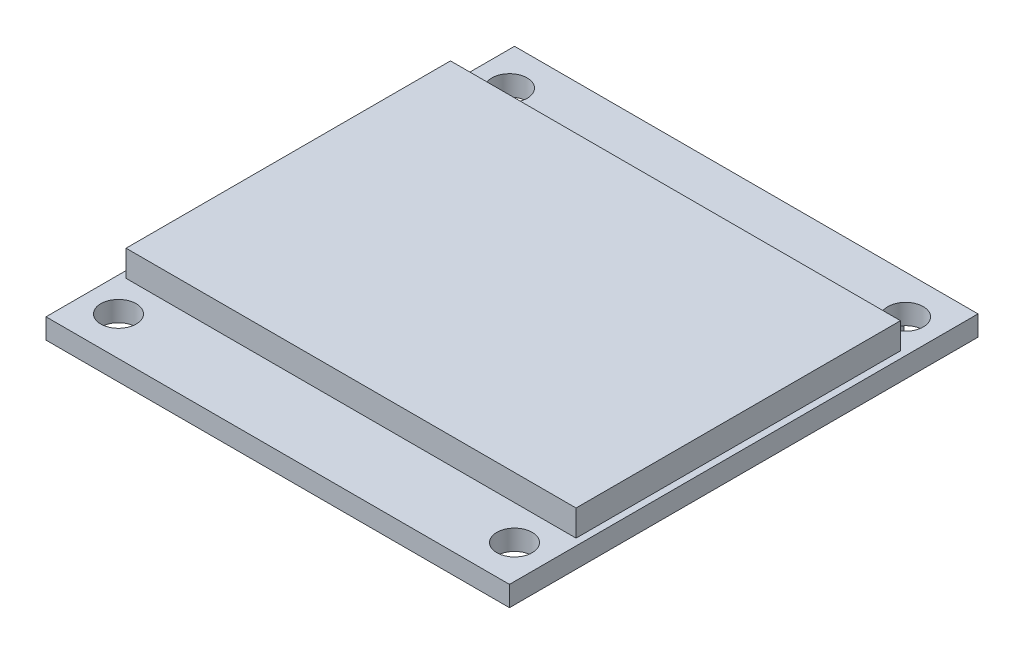
SolidWorks part; units mm, degrees
ref_plane "Front Plane" through (0, 0, 0) normal (0, 0, 1) x (1, 0, 0)
ref_plane "Top Plane" through (0, 0, 0) normal (0, 1, 0) x (1, 0, 0)
ref_plane "Right Plane" through (0, 0, 0) normal (1, 0, 0) x (0, 0, -1)
sketch "Sketch1" plane through (0, 0, 0) normal (0, 1, 0) x (1, 0, 0)
  line L1 (-21.737, 17.9787) -> (5.763, 17.9787)
  line L2 (-21.737, 17.9787) -> (-21.737, -9.8213)
  line L3 (-21.737, -9.8213) -> (5.763, -9.8213)
  line L4 (5.763, 17.9787) -> (5.763, -9.8213)
  circle A0 centre (-19.737, 15.6787) radius 1.05
  circle A1 centre (3.763, 15.6787) radius 1.05
  circle A2 centre (3.763, -7.5213) radius 1.05
  circle A3 centre (-19.737, -7.5213) radius 1.05
  dimension "D3" = 2.1
  dimension "D1" = 27.5
  dimension "D2" = 27.8
  dimension "D4" = 2
  dimension "D5" = 2
  dimension "D6" = 2.3
  dimension "D7" = 2.3
extrude "Boss-Extrude1" add sketch "Sketch1" along normal blind 1.2
sketch "Sketch2" plane through (0, 1.2, 0) normal (0, 1, 0) x (1, 0, 0)
  line L0 (5.763, 17.9787) -> (-21.737, 17.9787) construction
  line L1 (-21.337, 13.7787) -> (5.363, 13.7787)
  line L2 (-21.337, 13.7787) -> (-21.337, -5.4713)
  line L3 (-21.337, -5.4713) -> (5.363, -5.4713)
  line L4 (5.363, 13.7787) -> (5.363, -5.4713)
  line L5 (-21.737, 17.9787) -> (-21.737, -9.8213) construction
  line L6 (5.763, -9.8213) -> (5.763, 17.9787) construction
  dimension "D1" = 26.7
  dimension "D2" = 19.25
  dimension "D3" = 4.2
  dimension "D4" = 0.4
  dimension "D5" = 0.4
extrude "Boss-Extrude2" add sketch "Sketch2" along normal blind 1.55
sketch "Sketch3" plane through (0, 0, 0) normal (0, -1, 0) x (1, 0, 0)
  line L0 (5.763, -17.9787) -> (-21.737, -17.9787) construction
  line L1 (1.6187, -17.7287) -> (-16.1313, -17.7287)
  line L2 (1.6187, -17.7287) -> (1.6187, -15.1787)
  line L3 (1.6187, -15.1787) -> (-16.1313, -15.1787)
  line L4 (-16.1313, -17.7287) -> (-16.1313, -15.1787)
  dimension "D1" = 17.75
  dimension "D2" = 2.55
  dimension "D3" = 0.25
extrude "Boss-Extrude3" add sketch "Sketch3" along normal blind 2.35
